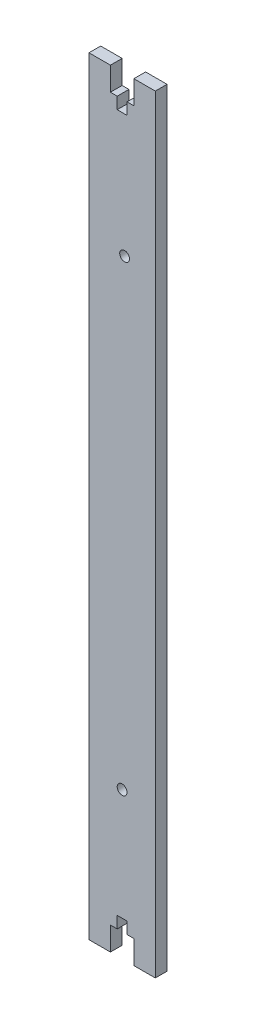
SolidWorks part; units mm, degrees
ref_plane "Front Plane" through (0, 0, 0) normal (0, 0, 1) x (1, 0, 0)
ref_plane "Top Plane" through (0, 0, 0) normal (0, 1, 0) x (1, 0, 0)
ref_plane "Right Plane" through (0, 0, 0) normal (1, 0, 0) x (0, 0, -1)
sketch "Sketch1" plane through (0, 0, 0) normal (0, 0, 1) x (1, 0, 0)
  line L1 (-14.14, 163.75) -> (14.14, 163.75)
  line L2 (-14.14, 163.75) -> (-14.14, -163.75)
  line L3 (-14.14, -163.75) -> (14.14, -163.75)
  line L4 (14.14, 163.75) -> (14.14, -163.75)
  line L5 (-14.14, 163.75) -> (14.14, -163.75) construction
  line L6 (-14.14, -163.75) -> (14.14, 163.75) construction
  point P0 (0, 0)
  dimension "D1" = 327.5
  dimension "D2" = 28.28
extrude "Boss-Extrude1" add sketch "Sketch1" along normal blind 5
sketch "Sketch2" plane through (0, 0, 5) normal (0, 0, 1) x (1, 0, 0)
  line L0 (0, 163.75) -> (0, 146.4815) construction
  line L1 (14.14, 163.75) -> (-14.14, 163.75) construction
  line L2 (0, 0) -> (-9.143, 0) construction
  line L3 (5, 163.75) -> (5, 153.75)
  line L4 (5, 153.75) -> (2.1, 153.75)
  line L5 (2.1, 153.75) -> (2.1, 148.75)
  line L6 (-2.1, 153.75) -> (-2.1, 148.75)
  line L7 (-5, 153.75) -> (-2.1, 153.75)
  line L8 (-5, 163.75) -> (-5, 153.75)
  line L9 (-5, 163.75) -> (5, 163.75)
  line L10 (2.1, 148.75) -> (-2.1, 148.75)
  line L11 (2.1, -148.75) -> (-2.1, -148.75)
  line L12 (-5, -163.75) -> (5, -163.75)
  line L13 (-5, -163.75) -> (-5, -153.75)
  line L14 (-5, -153.75) -> (-2.1, -153.75)
  line L15 (-2.1, -153.75) -> (-2.1, -148.75)
  line L16 (2.1, -153.75) -> (2.1, -148.75)
  line L17 (5, -153.75) -> (2.1, -153.75)
  line L18 (5, -163.75) -> (5, -153.75)
  line L19 (-16.2656, 96.25) -> (18.3826, 96.25) construction
  line L20 (-16.2656, 93.75) -> (-16.2656, 98.75) construction
  circle A0 centre (1.0585, 96.25) radius 2.1
  point P31 (0, 0)
  dimension "D5" = 4.2
  dimension "D1" = 10
  dimension "D2" = 2.9
  dimension "D3" = 5
  dimension "D4" = 5
extrude "Cut-Extrude1" cut sketch "Sketch2" against normal blind 10
sketch "Sketch3" plane through (0, 0, 5) normal (0, 0, 1) x (1, 0, 0)
  line L0 (-14.1443, -101.25) -> (14.14, -101.25) construction
  line L1 (-14.1443, -103.75) -> (-14.1443, -98.75) construction
  line L2 (14.14, -103.75) -> (14.14, -98.75) construction
  circle A0 centre (-0.0021, -101.25) radius 2.1
  dimension "D1" = 4.2
extrude "Cut-Extrude2" cut sketch "Sketch3" against normal blind 10
